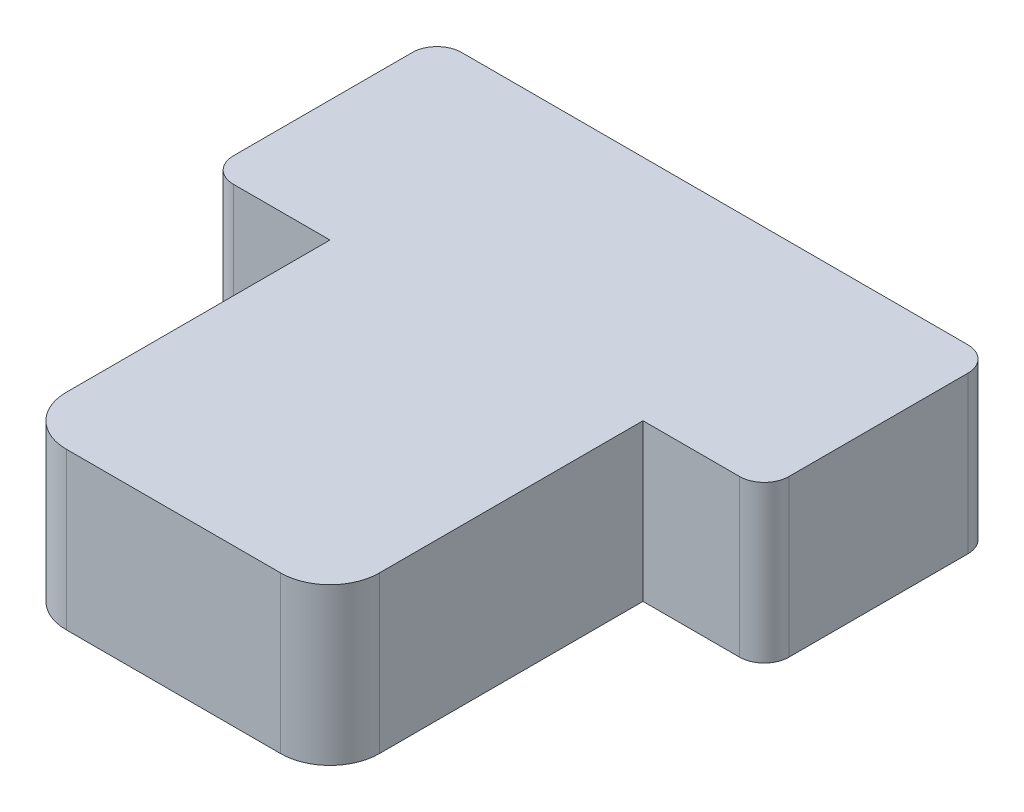
SolidWorks part; units mm, degrees
material "Beech"
ref_plane "Front Plane" through (0, 0, 0) normal (0, 0, 1) x (1, 0, 0)
ref_plane "Top Plane" through (0, 0, 0) normal (0, 1, 0) x (1, 0, 0)
ref_plane "Right Plane" through (0, 0, 0) normal (1, 0, 0) x (0, 0, -1)
sketch "Sketch1" plane through (0, 0, 0) normal (0, 1, 0) x (1, 0, 0)
  line L0 (0, 0) -> (6.35, 0)
  line L1 (0, 0) -> (0, 6.35)
  line L2 (6.35, 0) -> (6.35, 6.35)
  line L4 (-2.46, 10.9807) -> (-2.46, 6.35)
  line L5 (-2.46, 10.9807) -> (8.81, 10.9807)
  line L6 (-2.46, 6.35) -> (0, 6.35)
  line L7 (8.81, 10.9807) -> (8.81, 6.35)
  line L8 (6.35, 6.35) -> (8.81, 6.35)
  dimension "D1" = 6.35
  dimension "D2" = 6.35
  dimension "D3" = 11.27
  dimension "D4" = 4.6307
extrude "MotorSupport_Extrude" add sketch "Sketch1" along normal blind 3.175
fillet "MotorSupport_BottomFillet" radius 1 2 edges at (0, 1.5875, 0) (6.35, 1.5875, 0)
fillet "MotorSupport_TopFillet" radius 0.5 4 edges at (-2.46, 1.5875, -6.35) (-2.46, 1.5875, -10.9807) (8.81, 1.5875, -10.9807) (8.81, 1.5875, -6.35)
equation "\"CageLeftBottomEdge\"=22.11mm"
equation "\"CageLeftTopEdge\"=22.11mm"
equation "\"CageRightBottomEdge\"=21.63mm"
equation "\"CageRightTopEdge\"=21.63mm"
equation "\"CageHeight\"=86.04mm"
equation "\"CageLength\"=73.76mm"
equation "\"CageTopScrewClearance\"=10mm"
equation "\"CageBottomScrewClearance\"=25mm"
equation "\"CageLeftTopDepth\"= 11.65mm"
equation "\"CageLeftBottomDepth\"=11.11mm"
equation "\"CageLeftTopHeight\"=8.56175mm"
equation "\"CageLeftBottomHeight\"=16mm"
equation "\"CageRightTopDepth\"= 11.05mm"
equation "\"CageRightBottomDepth\"=10.58mm"
equation "\"CageRightTopHeight\"=9.6mm"
equation "\"CageRightBottomHeight\"=15.49mm"
equation "\"CageLeftTopChannelDepth\"=2.41908mm"
equation "\"CageLeftBottomChannelDepth\"=2.588mm"
equation "\"CageLeftChannelHeight\"=11.7mm"
equation "\"CageRightTopChannelDepth\"=2.32mm"
equation "\"CageRightBottomChannelDepth\"=2.318mm"
equation "\"CageRightChannelHeight\"=10mm"
equation "\"CageChanRelHeight\"=23.99mm"
equation "\"CageChanRelDepth\"=5.492mm"
equation "\"CageChamberRadius\"=16.261mm"
equation "\"CageScrewDiameter\"=4.8mm"
equation "\"CageSetScrewDiameter\"=3.5mm"
equation "\"CageAxleRadius\"=6.639mm"
equation "\"CageAxleKeyHeight\"=1.619mm"
equation "\"CageAxleKeyWidth\"=2.662mm"
equation "\"CageHoseWindowWidth\"=16.29mm"
equation "\"CageHoseWindowHeight\"=26.5mm"
equation "\"CageHoseWindow-Edge\"=8.89mm"
equation "\"CageScrew-VerticalEdge\"=5.0mm"
equation "\"CageScrew-HorizontalEdge\"=7.5mm"
equation "\"CageScrew-HoseCornerScrewEdge\"=4.45mm"
equation "\"CageAxle-BottomEdge\"=56.05mm"
equation "\"CageAxle-FrontEdge\"=46.03mm"
equation "\"CageBackSetScrew-Axle\"=40mm"
equation "\"CageFrontSetScrew-Axle\"=22mm"
equation "\"CageVelocityWindow-BackEdge\"=34.8mm"
equation "\"CageVelocityWindow-BottomEdge\"=27.55mm"
equation "\"CageVelocityWindowHeight\"=22.29mm"
equation "\"CageVelocityWindowWidth\"=12.61mm"
equation "\"TriggerSlot-BottomEdge\"=6.35mm"
equation "\"TriggerSlot-FrontEdge\"=15mm"
equation "\"TriggerSlotSize\"=6.7mm"
equation "\"TriggerRackOffset\"=.236224in"
equation "\"TriggerSlotSizeInt\"=.25in"
equation "\"MotorMountLegLength\"=.25in"
equation "\"GearOffset\"=.264907in"
equation "\"TriggerSlotSpacing\"=.25in"
equation "\"whitemotordepth\"=11.27mm"
equation "\"whitemotorbackdepth\"=3.845mm"
equation "\"whitemotoraxledepth\" = 3.5mm"
equation "\"whitemotoraxleoffset\"=11.4mm"
equation "\"whitemotorwidth\"=12.07mm"
equation "\"whitemotorheight\"=16.68mm"
equation "\"whitemotorcylinderlength\" =13.04mm"
equation "\"whitemotorcylinderradius\"=3.845mm"
equation "\"whitemotorcylinderoffset\"=2.35mm"
equation "\"whitemotorcutoutlength\"=1.88mm"
equation "\"whitemotorouterrad\"=5mm"
equation "\"whitemotorinnerrad\"=2.95mm"
equation "\"D1@Sketch1\"=\"TriggerSlotSizeInt\""
equation "\"D2@Sketch1\"=\"MotorMountLegLength\""
equation "\"D3@Sketch1\"=\"whitemotordepth\""
equation "\"D4@Sketch1\"=\"GearOffset\"+\"TriggerRackOffset\"-\"whitemotoraxleoffset\"+\"elasticdepth\"+.005in"
equation "\"D1@MotorSupport_Extrude\"=.125in"
equation "\"TriggerMiniSlotWidth\"=3.5mm"
equation "\"TriggerRackWidth\"=6.5mm"
equation "\"elasticracklength\"=2in"
equation "\"elasticrackpegsize\"=.25in"
equation "\"elasticrackpegbuffer\"=.125in"
equation "\"elasticrackpegspacing\"=1.76476378in"
equation "\"elasticbaybuffer\"=.25in"
equation "\"elasticdepth\"=.125in"
equation "\"elasticbaydepth\"=.75in"
equation "\"motormountwidth\"=12mm"
equation "\"motormountcornerfillet\"=3mm"
equation "\"pandiscradius\"=14in"
equation "\"towermaterialwidth\"=.25in"
equation "\"towerslotlength\"=.5in"
equation "\"towermarkerspace\"=5in"
equation "\"towerslothorizoffset\"=1in"
equation "\"towerslothorizspacing\"=2in"
equation "\"towerslotvertoffset\"=3in"
equation "\"towerslotvertspacing\"=1in"
equation "\"towerheight\"=12in"
equation "\"towerupslot\"=1in"
equation "\"toweraxle\"=.5in"
equation "\"stepperouterrad\"=10mm"
equation "\"stepperscrewsize\"=3.45mm"
equation "\"stepperscrewc2c\"=49.5mm"
equation "\"stepperdepthoffset\"=24mm"
equation "\"stepperhorizoffset\"=22.91mm"
equation "\"shaftslotOD\"=18.8mm"
equation "\"shaftslotID\"=13.28mm"
equation "\"shaftkeywidth\"=2.67mm"
equation "\"shaftkeydepth\"=1.8mm"
equation "\"shaftcollartotaldepth\"=12.5mm"
equation "\"shaftsquaredepth\"=6mm"
equation "\"shaftsetscrewsize\"=3.5mm"
equation "\"shaftkeytightdepth\"=1.85mm"
equation "\"shaftslottightID\"=12.78mm"
equation "\"shaftsetscrewoffset\"=9mm"
equation "\"cagecollartotaldepth\"=10mm"
equation "\"cagecollartotalwidth\"=35mm"
equation "\"cagecollarbasedepth\"=4mm"
equation "\"gearhubintdiam\"=30mm"
equation "\"gearhubintwid\"=15mm"
equation "\"towerspeedwidth\"=2in"
equation "\"towerspeedheight\"=8in"
equation "\"towerspeedgap\"=2in"
equation "\"stepperaxleflat\"=.037in"
equation "\"stepperaxlerad\"=0.11811024in"
equation "\"ajaxaxlesize\"=3.87mm"
equation "\"ajaxinnercut\"=2.3mm"
equation "\"ajaxwidth\"=6.1mm"
equation "\"ajaxdiametral\"=25.8854"
equation "\"ajaxcutoutdepth\"=2.3mm"
equation "\"ajax4020gap\"=29.5mm"
equation "\"ajax4010gap\"=24.5mm"
equation "\"ajax20hubbuffer\"=0.240157in"
equation "\"ajax20hubholeoffset\"=.19685in"
equation "\"ajax20hubholesize\"=.059055in"
equation "\"ajax20cutoutint\"=13.4mm"
equation "\"ajax40hubholesize\"=7.21mm"
equation "\"ajax40hubholeoffset\"=10mm"
equation "\"ajax40hubbuffer\"=.350394in"
equation "\"ajax40cutoutint\"=32.6mm"
equation "\"bearingpandiscrad\"=6.8in"
equation "\"bearingpandiscang\"=48.75deg"
equation "\"bearingclearholedist\"=4.7345in"
equation "\"bearingclearholesize\"=.5in"
equation "\"bearingclearholeang\"=22.5deg"
equation "\"bearingmountholedist\"=4.25in"
equation "\"bearingwirehole\"=1.5in"
equation "\"no6diam\"=.146in"
equation "\"shortconangle\"=20deg"
equation "\"shortconlen\"=.875in"
equation "\"longconlen\"=1.25in"
equation "\"longconangle\"=15deg"
equation "\"TGMGearFaceDiameter\"=24.40mm"
equation "\"TGMCylinderLength\"=15.00mm"
equation "\"TGMScrewHole-Center\"=8.70mm"
equation "\"TGMScrewHoleDiameter\"=5.04mm"
equation "\"TGMCenterHoleDiameter\"=9.50mm"
equation "\"TGMShaftCollarSideLength\"=19.00mm"
equation "\"TGMShaftCollarDockingDepth\"=7.00mm"
equation "\"towerplatslotoffset\"=1.5in"
equation "\"towermotorpanelheight\"=10in"
equation "\"towerplatdepth\"=2in"
equation "\"ajaxhubdepth\"=.25in"
equation "\"shconangle\"=20deg"
equation "\"shconlen\"=1in"
equation "\"lnconlen\"=1.5in"
equation "\"lnconangle\"=15deg"
